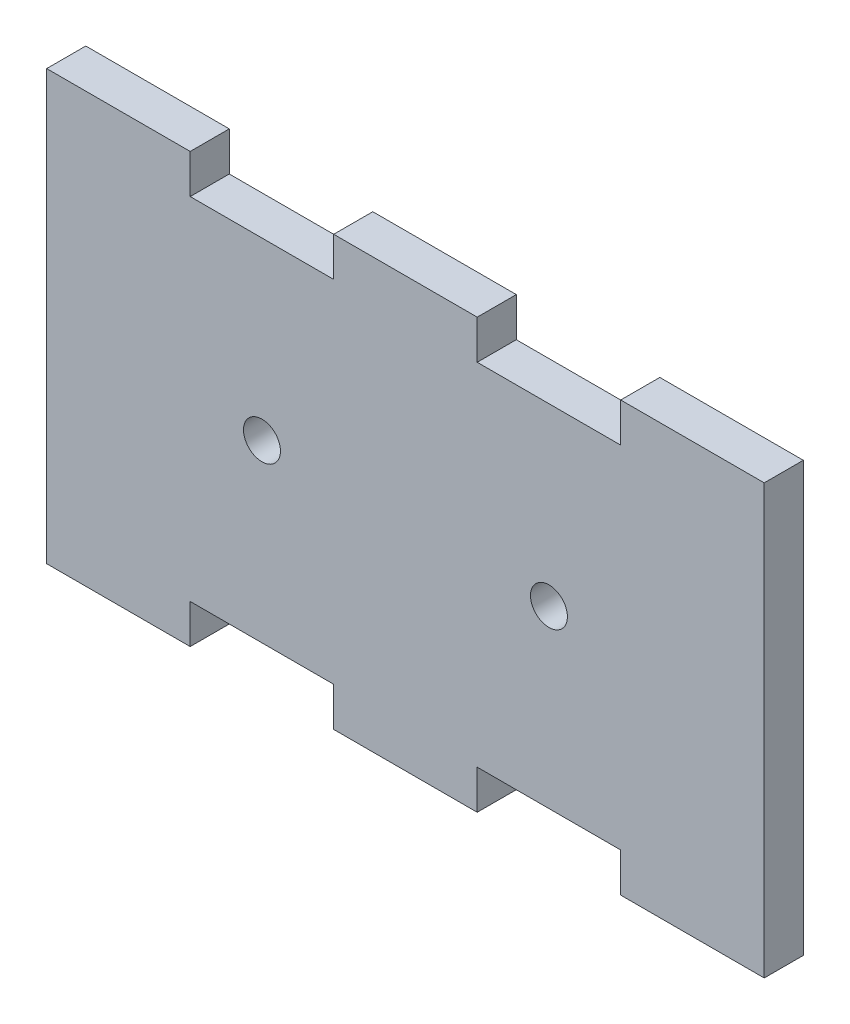
SolidWorks part; units mm, degrees
ref_plane "Front Plane" through (0, 0, 0) normal (0, 0, 1) x (1, 0, 0)
ref_plane "Top Plane" through (0, 0, 0) normal (0, 1, 0) x (1, 0, 0)
ref_plane "Right Plane" through (0, 0, 0) normal (1, 0, 0) x (0, 0, -1)
sketch "Sketch1" plane through (0, 0, 0) normal (0, 0, 1) x (1, 0, 0)
  line L0 (18.985, 0) -> (29.14, 0)
  line L1 (0, 0) -> (15.985, 0)
  line L2 (0, 0) -> (0, 14.24)
  line L3 (11.656, 14.24) -> (23.312, 14.24)
  line L4 (29.14, 0) -> (29.14, 14.24)
  line L6 (0, 14.24) -> (0, 17.415)
  line L7 (0, 17.415) -> (11.656, 17.415)
  line L8 (11.656, 14.24) -> (11.656, 17.415)
  line L10 (29.14, 14.24) -> (29.14, 17.415)
  line L11 (29.14, 17.415) -> (23.312, 17.415)
  line L12 (23.312, 14.24) -> (23.312, 17.415)
  arc A0 (18.985, 0) -> (15.985, 0) centre (17.485, 0) ccw
  dimension "D6" = 3
  dimension "D1" = 29.14
  dimension "D2" = 11.656
  dimension "D3" = 11.655
  dimension "D4" = 3.175
  dimension "D5" = 14.24
extrude "Boss-Extrude1" add sketch "Sketch1" along normal blind 3.175
mirror "Mirror1" about plane through (0, 0, 3.175) normal (0, 1, 0) of bodies 101
mirror "Mirror3" about plane through (29.14, 14.24, 3.175) normal (-1, 0, 0) of bodies 102
